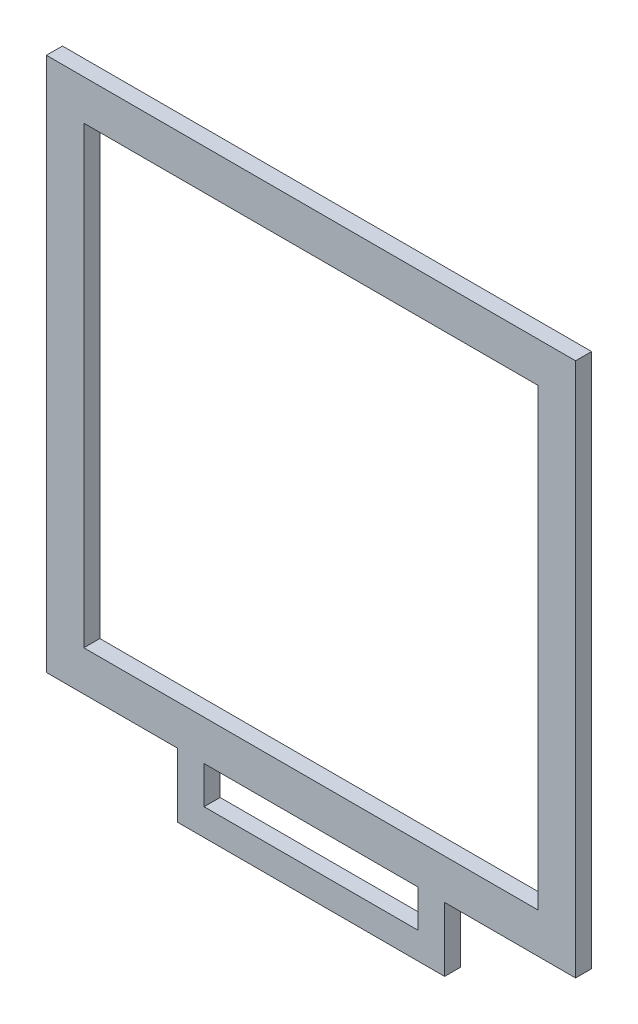
SolidWorks part; units mm, degrees
ref_plane "Alzado" through (0, 0, 0) normal (0, 0, 1) x (1, 0, 0)
ref_plane "Planta" through (0, 0, 0) normal (0, 1, 0) x (1, 0, 0)
ref_plane "Vista lateral" through (0, 0, 0) normal (1, 0, 0) x (0, 0, -1)
sketch "Croquis1" plane through (0, 0, 0) normal (0, 0, 1) x (1, 0, 0)
  line L1 (0, 100) -> (99, 100)
  line L2 (0, 100) -> (0, 0)
  line L3 (0, 0) -> (99, 0)
  line L4 (99, 100) -> (99, 0)
  line L5 (7, 7.5) -> (92, 7.5)
  line L6 (7, 7.5) -> (7, 92.5)
  line L7 (7, 92.5) -> (92, 92.5)
  line L8 (92, 7.5) -> (92, 92.5)
  line L9 (7, 7.5) -> (92, 92.5) construction
  line L10 (7, 92.5) -> (92, 7.5) construction
  point P6 (49.5, 50)
  point P7 (49.5, 0)
  point P9 (99, 50)
  dimension "D3" = 85
  dimension "D1" = 100
  dimension "D2" = 99
extrude "Saliente-Extruir1" add sketch "Croquis1" along normal blind 3
sketch "Croquis2" plane through (0, 0, 3) normal (0, 0, 1) x (1, 0, 0)
  line L0 (24.5, 0) -> (29.5, 0)
  line L1 (0, 0) -> (99, 0) construction
  line L2 (29.5, 0) -> (29.5, -7)
  line L3 (29.5, -7) -> (69.5, -7)
  line L4 (69.5, -7) -> (69.5, 0)
  line L5 (69.5, 0) -> (74.5, 0)
  line L6 (74.5, 0) -> (74.5, -12)
  line L7 (74.5, -12) -> (24.5, -12)
  line L8 (24.5, -12) -> (24.5, 0)
  point P10 (49.5, 0)
  point P11 (49.5, -7)
  dimension "D1" = 5
  dimension "D2" = 5
  dimension "D3" = 5
  dimension "D4" = 50
  dimension "D5" = 12
extrude "Saliente-Extruir2" add sketch "Croquis2" against normal blind 3
